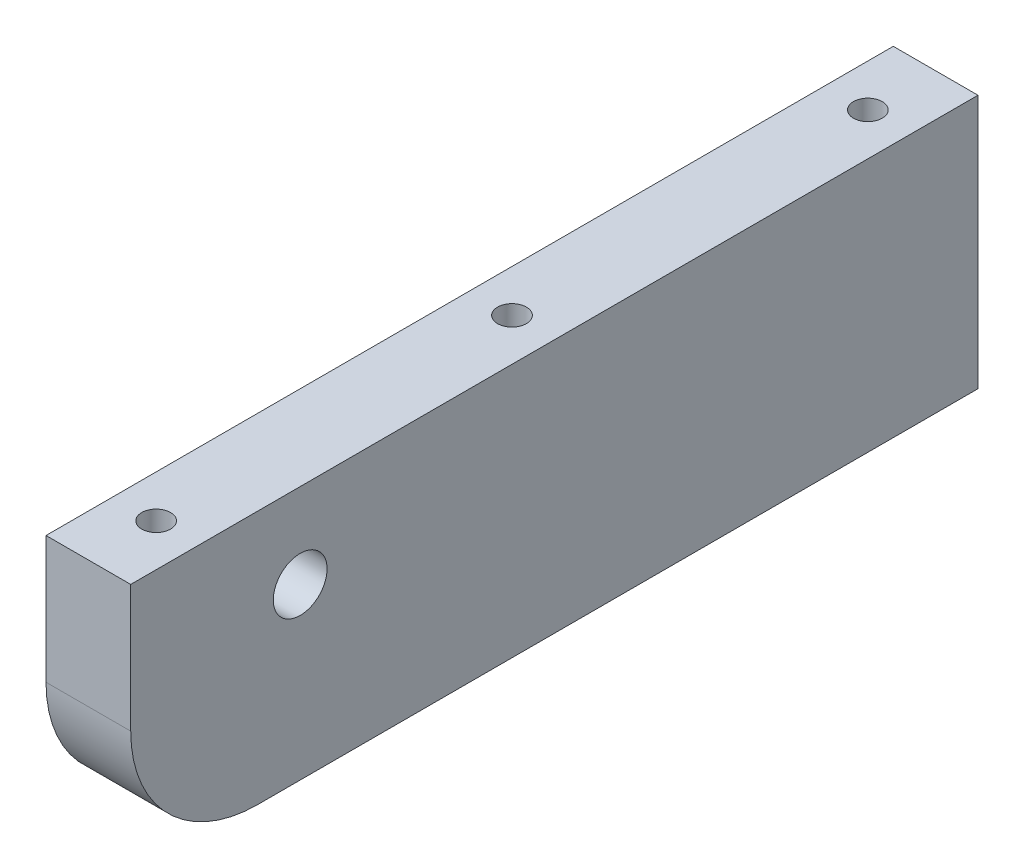
SolidWorks part; units mm, degrees
ref_plane "Front Plane" through (0, 0, 0) normal (0, 0, 1) x (1, 0, 0)
ref_plane "Top Plane" through (0, 0, 0) normal (0, 1, 0) x (1, 0, 0)
ref_plane "Right Plane" through (0, 0, 0) normal (1, 0, 0) x (0, 0, -1)
sketch "Sketch1" plane through (0, 0, 0) normal (1, 0, 0) x (0, 0, -1)
  line L1 (-50, -15) -> (50, -15)
  line L2 (-50, -15) -> (-50, 15)
  line L3 (-50, 15) -> (50, 15)
  line L4 (50, -15) -> (50, 15)
  line L5 (-50, -15) -> (50, 15) construction
  line L6 (-50, 15) -> (50, -15) construction
  circle A1 centre (-30, 5) radius 3.175
  point P0 (0, 0)
  dimension "D3" = 6.35
  dimension "D1" = 30
  dimension "D2" = 100
  dimension "D4" = 10
  dimension "D5" = 20
extrude "Boss-Extrude1" add sketch "Sketch1" along normal blind 10
fillet "Fillet1" radius 15 1 edges at (5, -15, 50)
hole_wizard "CBORE for M3 SHCS" positions "Sketch2" profile "Sketch3" counterbore size "M3" standard "ANSI Metric"
sketch "Sketch2" plane through (-616.2935, 25, -1323.2827) normal (0, 1, 0) x (1, 0, 0)
  line L3 (621.2935, -1281.2827) -> (621.2935, -1365.2827) construction
  line L5 (731.2935, -1281.2827) -> (731.2935, -1359.2827) construction
  circle A0 centre (731.2935, -1281.2827) radius 2.243
  circle A1 centre (731.2935, -1359.2827) radius 2.2384
  circle A3 centre (621.2935, -1281.2827) radius 2.3325
  circle A4 centre (621.2935, -1365.2827) radius 1.7576
  circle A5 centre (621.2935, -1323.2827) radius 1.8624
  circle A6 centre (731.2935, -1320.2827) radius 2.0271
  point P1 (731.2935, -1281.2827)
  point P8 (731.2935, -1359.2827)
  point P15 (621.2935, -1281.2827)
  point P17 (621.2935, -1365.2827)
  point P19 (621.2935, -1323.2827)
  point P27 (731.2935, -1320.2827)
sketch "Sketch3" plane through (115, 25, -42) normal (1, 0, 0) x (0, 0, 1)
  line L0 (0, 0) -> (0, 24.0215)
  line L1 (0, 24.0215) -> (1.7, 23)
  line L2 (1.7, 23) -> (1.7, 3)
  line L3 (1.7, 3) -> (3.25, 3)
  line L4 (3.25, 3) -> (3.25, 0)
  line L5 (3.25, 0) -> (0, 0)
  line L6 (0, 24.0215) -> (-1.7, 23) construction
  line L7 (0, -6.35) -> (0, 107.95) construction
  dimension "Hole Dia." = 3.4
  dimension "Hole Depth" = 23
  dimension "C'Bore Dia." = 6.5
  dimension "C'Bore Depth" = 3
  dimension "Drill Angle" = 118
